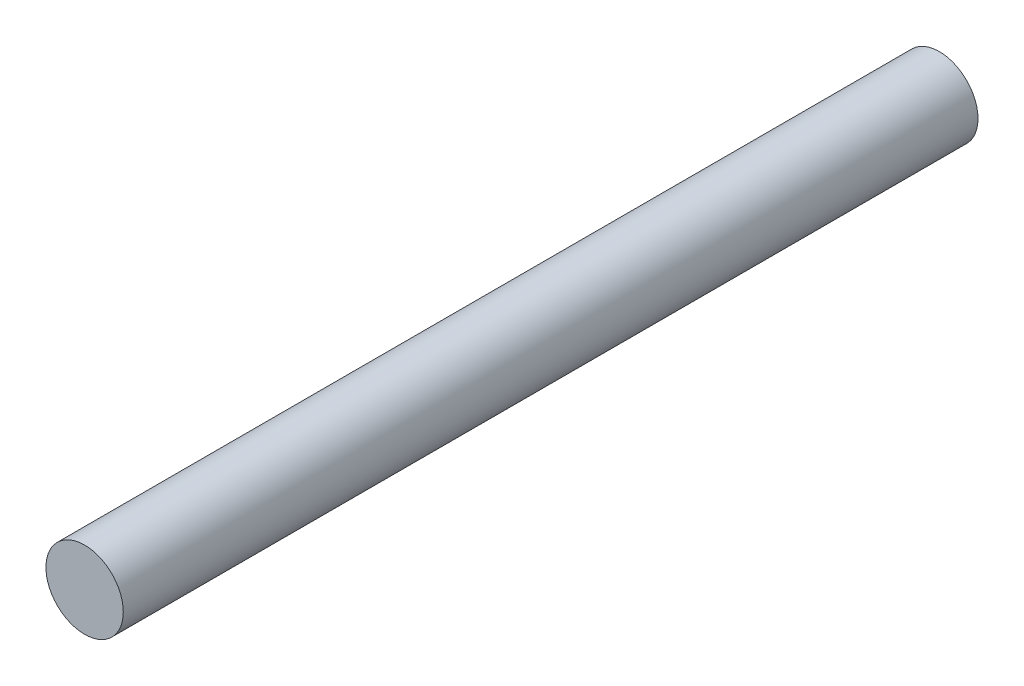
SolidWorks part; units mm, degrees
ref_plane "Front Plane" through (0, 0, 0) normal (0, 0, 1) x (1, 0, 0)
ref_plane "Top Plane" through (0, 0, 0) normal (0, 1, 0) x (1, 0, 0)
ref_plane "Right Plane" through (0, 0, 0) normal (1, 0, 0) x (0, 0, -1)
sketch "Sketch1" plane through (0, 0, 0) normal (0, 0, 1) x (1, 0, 0)
  circle A0 centre (0, 0) radius 3
  dimension "D1" = 6
extrude "Boss-Extrude1" add sketch "Sketch1" along normal blind 66.3
